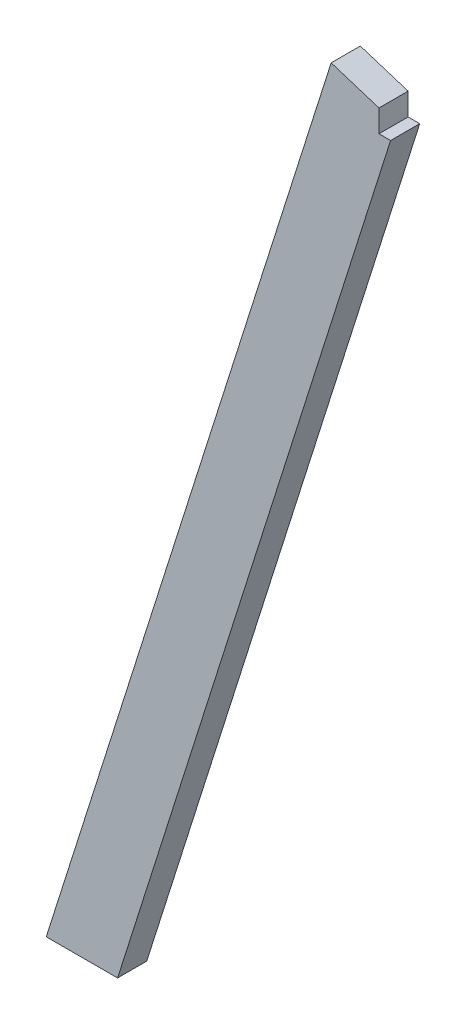
SolidWorks part; units mm, degrees
ref_plane "Front Plane" through (0, 0, 0) normal (0, 0, 1) x (1, 0, 0)
ref_plane "Top Plane" through (0, 0, 0) normal (0, 1, 0) x (1, 0, 0)
ref_plane "Right Plane" through (0, 0, 0) normal (1, 0, 0) x (0, 0, -1)
sketch "Sketch2" plane through (0, 0, 0) normal (0, 0, 1) x (1, 0, 0)
  line L0 (0, 0) -> (93.2542, 0)
  line L1 (0, 0) -> (372.4509, 1175.6969)
  line L2 (93.2542, 0) -> (457.2, 1148.8491)
  line L4 (457.2, 1148.8491) -> (372.4509, 1175.6969)
  point P0 (46.6271, 0)
  dimension "D1" = 88.9
  dimension "D2" = 1219.2
  dimension "D3" = 457.2
  dimension "D4" = 72.422
extrude "Boss-Extrude1" add sketch "Sketch2" along normal blind 38.1
sketch "Sketch3" plane through (0, 0, 38.1) normal (0, 0, 1) x (1, 0, 0)
  line L0 (93.2542, 0) -> (457.2, 1148.8491) construction
  line L1 (457.2, 1148.8491) -> (372.4509, 1175.6969) construction
  line L2 (93.2542, 0) -> (457.2, 1148.8491)
  line L3 (457.2, 1148.8491) -> (372.4509, 1175.6969)
  line L5 (434.975, 1171.0741) -> (479.425, 1171.0741)
  line L6 (434.975, 1171.0741) -> (434.975, 1126.6241)
  line L7 (434.975, 1126.6241) -> (479.425, 1126.6241)
  line L8 (479.425, 1171.0741) -> (479.425, 1126.6241)
  line L9 (434.975, 1171.0741) -> (479.425, 1126.6241) construction
  line L10 (434.975, 1126.6241) -> (479.425, 1171.0741) construction
  circle A0 centre (457.2, 1148.8491) radius 22.225 construction
  line M4 (457.2, 1148.8491) -> (372.4509, 1175.6969)
  dimension "D1" = 44.45
extrude "Cut-Extrude1" cut sketch "Sketch3" against normal through all contours L6 L7 L2 M4
